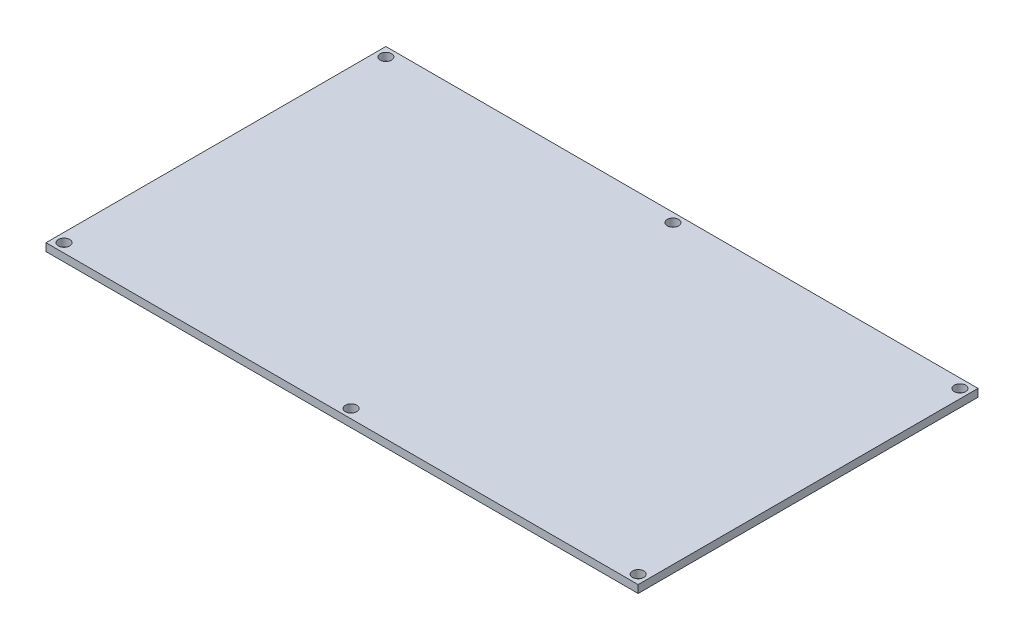
SolidWorks part; units mm, degrees
material "1060 合金"
ref_plane "前视基准面" through (0, 0, 0) normal (0, 0, 1) x (1, 0, 0)
ref_plane "上视基准面" through (0, 0, 0) normal (0, 1, 0) x (1, 0, 0)
ref_plane "右视基准面" through (0, 0, 0) normal (1, 0, 0) x (0, 0, -1)
sketch "草图1" plane through (0, 0, 0) normal (0, 1, 0) x (1, 0, 0)
  line L1 (115, 66) -> (-115, 66)
  line L2 (115, 66) -> (115, -66)
  line L3 (115, -66) -> (-115, -66)
  line L4 (-115, 66) -> (-115, -66)
  line L5 (115, 66) -> (-115, -66) construction
  line L6 (115, -66) -> (-115, 66) construction
  point P0 (0, 0)
  dimension "D1" = 230
  dimension "D2" = 132
extrude "凸台-拉伸1" add sketch "草图1" along normal blind 3
sketch "草图2" plane through (0, 3, 0) normal (0, 1, 0) x (1, 0, 0)
  line L0 (115, 66) -> (-115, 66) construction
  line L1 (-115, -66) -> (115, -66) construction
  line L2 (-115, 66) -> (-115, -66) construction
  line L3 (115, -66) -> (115, 66) construction
  circle A0 centre (-111.5, 62.5) radius 2.2
  circle A1 centre (0, 62.5) radius 2.2
  circle A2 centre (111.5, 62.5) radius 2.2
  circle A3 centre (111.5, -62.5) radius 2.2
  circle A4 centre (0, -62.5) radius 2.2
  circle A5 centre (-111.5, -62.5) radius 2.2
  point P0 (-111.5, 62.5)
  point P1 (0, 62.5)
  point P2 (111.5, 62.5)
  point P3 (111.5, -62.5)
  point P4 (0, -62.5)
  point P5 (-111.5, -62.5)
  dimension "D1" = 3.5
  dimension "D2" = 3.5
  dimension "D3" = 3.5
  dimension "D4" = 3.5
extrude "切除-拉伸1" cut sketch "草图2" against normal blind 4
equation "\"3。5\"=10.144"
